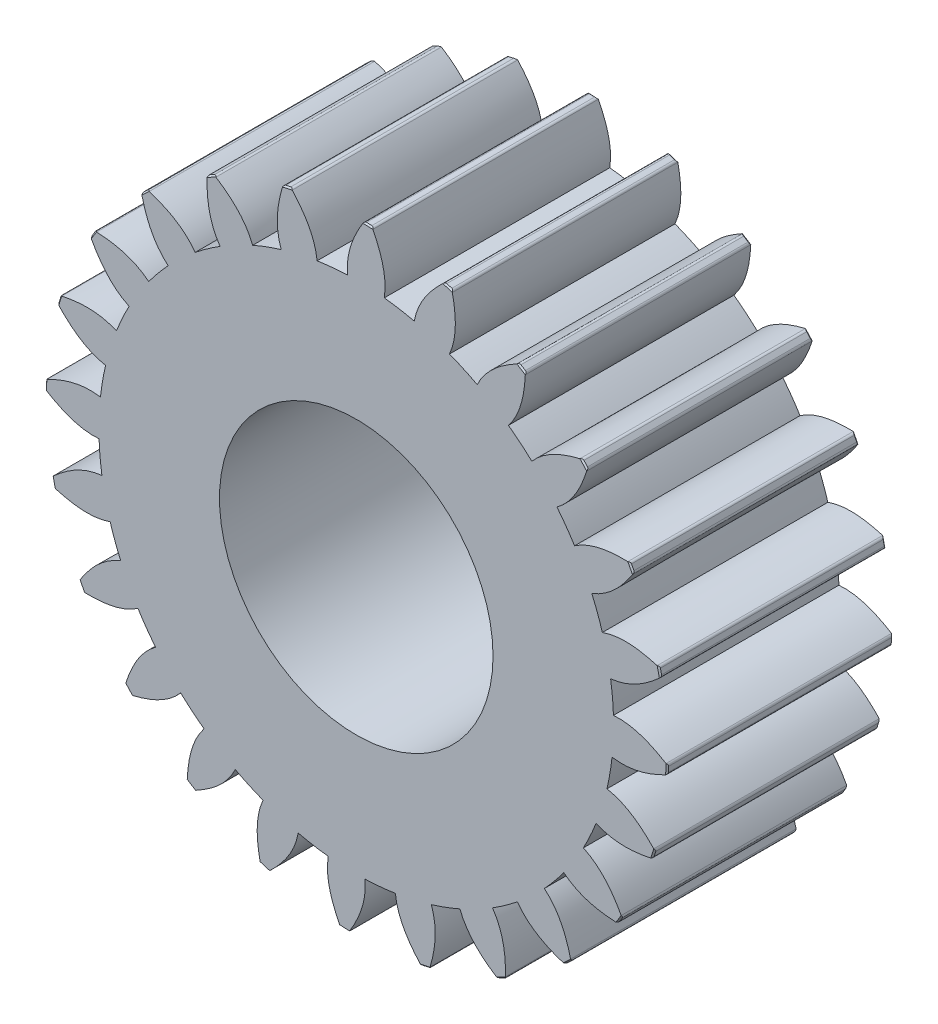
SolidWorks part; units mm, degrees
ref_plane "Front Plane" through (0, 0, 0) normal (0, 0, 1) x (1, 0, 0)
ref_plane "Top Plane" through (0, 0, 0) normal (0, 1, 0) x (1, 0, 0)
ref_plane "Right Plane" through (0, 0, 0) normal (1, 0, 0) x (0, 0, -1)
sketch "Sketch1" plane through (0, 0, 0) normal (0, 0, 1) x (1, 0, 0)
  line L0 (-11.4128, 37.6847) -> (-8.6978, 38.1063) construction
  line L1 (-0.553, 39.3711) -> (10.35, 37.9904) construction
  line L2 (10.35, 37.9904) -> (20.4466, 33.6501) construction
  line L3 (20.4466, 33.6501) -> (28.9504, 26.6883) construction
  line L4 (-0.553, 39.3711) -> (-11.5419, 39.2168) construction
  line L5 (10.35, 37.9904) -> (-10.8571, 43.768) construction
  line L6 (20.4466, 33.6501) -> (-7.7297, 50.7707) construction
  line L7 (28.9504, 26.6883) -> (-0.8457, 59.0098) construction
  line L8 (0, 0) -> (-5.7735, 37.1794) construction
  line L9 (-11.4128, 37.6847) -> (-8.6978, 38.1063)
  line L10 (0, 0) -> (-8.6978, 38.1063) construction
  circle A0 centre (0, 0) radius 39.375
  arc A1 (-9.5233, 44.4922) -> (-10.725, 44.2179) centre (0, 0) ccw
  circle A2 centre (0, 0) radius 42 construction
  circle A3 centre (0, 0) radius 37.625
  spline S0 degree 3 poles (-10.98, 35.9872) (-11.1806, 36.5485) (-11.4483, 37.6219) (-11.6575, 40.2358) (-11.2493, 42.4379) (-10.7704, 44.0684) (-10.725, 44.2179) knots -0.070067 -0.070067 -0.070067 -0.070067 0 0.062637 0.25014 0.269136 0.269136 0.269136 0.269136
  spline S1 degree 3 poles (-5.7222, 37.1873) (-5.785, 37.78) (-6.0096, 38.8632) (-6.9553, 41.3091) (-8.2785, 43.116) (-9.4175, 44.3772) (-9.5233, 44.4922) knots -0.070067 -0.070067 -0.070067 -0.070067 0 0.062637 0.25014 0.269136 0.269136 0.269136 0.269136
  dimension "D1" = 91
  dimension "D2" = 84
  dimension "D3" = 78.75
  dimension "D4" = 75.25
  dimension "D5" = 10.99
  dimension "D6" = 10.99
  dimension "D7" = 21.98
  dimension "D8" = 32.97
  dimension "D9" = 43.96
extrude "Boss-Extrude1" add sketch "Sketch1" along normal blind 32.97
chamfer "Chamfer1" distance 0.2 angle 45 2 edges at (-10.1251, 44.3591, 32.97) (-10.1251, 44.3591, 0)
fillet "Fillet1" radius 0.4 2 edges at (-9.5233, 44.4922, 16.485) (-10.725, 44.2179, 16.485)
pattern_circular "CirPattern1" count 24 over 360 about axis through (0, 0, 32.97) along (0, 0, 1) of "Fillet1", "Boss-Extrude1", "Chamfer1"
sketch "Sketch2" plane through (0, 0, 32.97) normal (0, 0, 1) x (1, 0, 0)
  circle A0 centre (0, 0) radius 20
  dimension "D1" = 40
extrude "Cut-Extrude1" cut sketch "Sketch2" against normal through all
